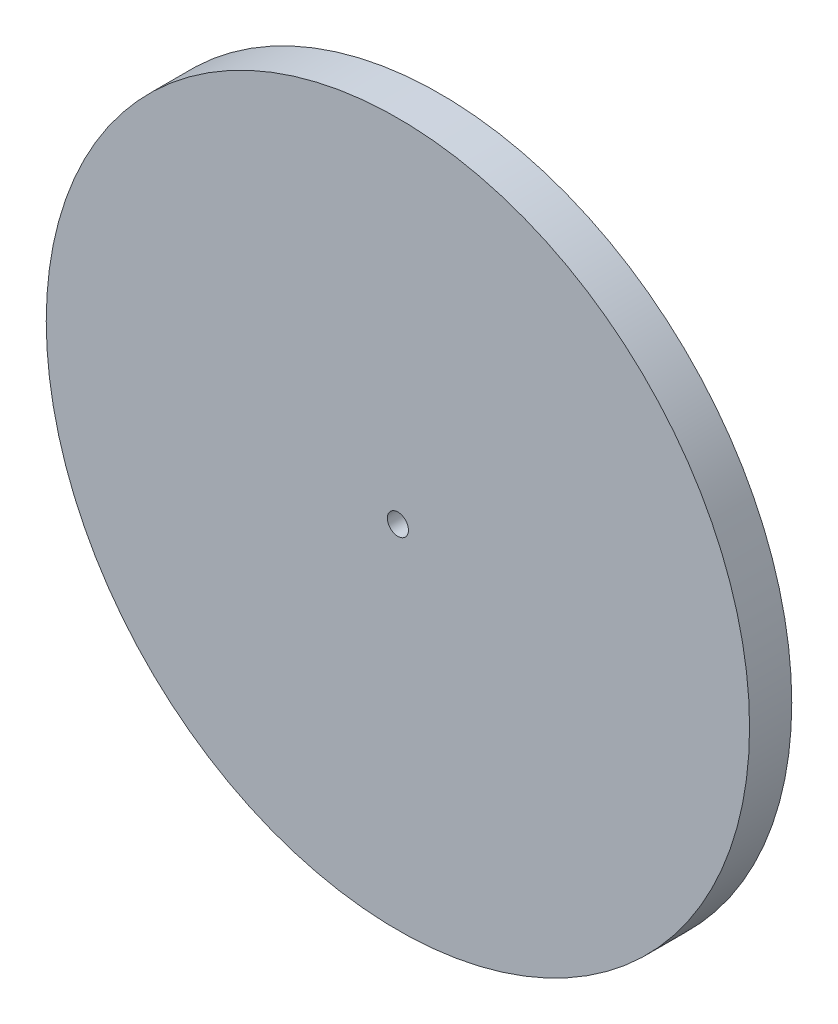
SolidWorks part; units mm, degrees
material "Free-Cutting Brass, UNS C36000"
ref_plane "Front Plane" through (0, 0, 0) normal (0, 0, 1) x (1, 0, 0)
ref_plane "Top Plane" through (0, 0, 0) normal (0, 1, 0) x (1, 0, 0)
ref_plane "Right Plane" through (0, 0, 0) normal (1, 0, 0) x (0, 0, -1)
sketch "Sketch1" plane through (0, 0, 0) normal (0, 0, 1) x (1, 0, 0)
  circle A0 centre (0, 0) radius 25
  circle A1 centre (0, 0) radius 0.75
  dimension "D1" = 50
  dimension "D2" = 1.5
extrude "Boss-Extrude1" add sketch "Sketch1" along normal blind 3
